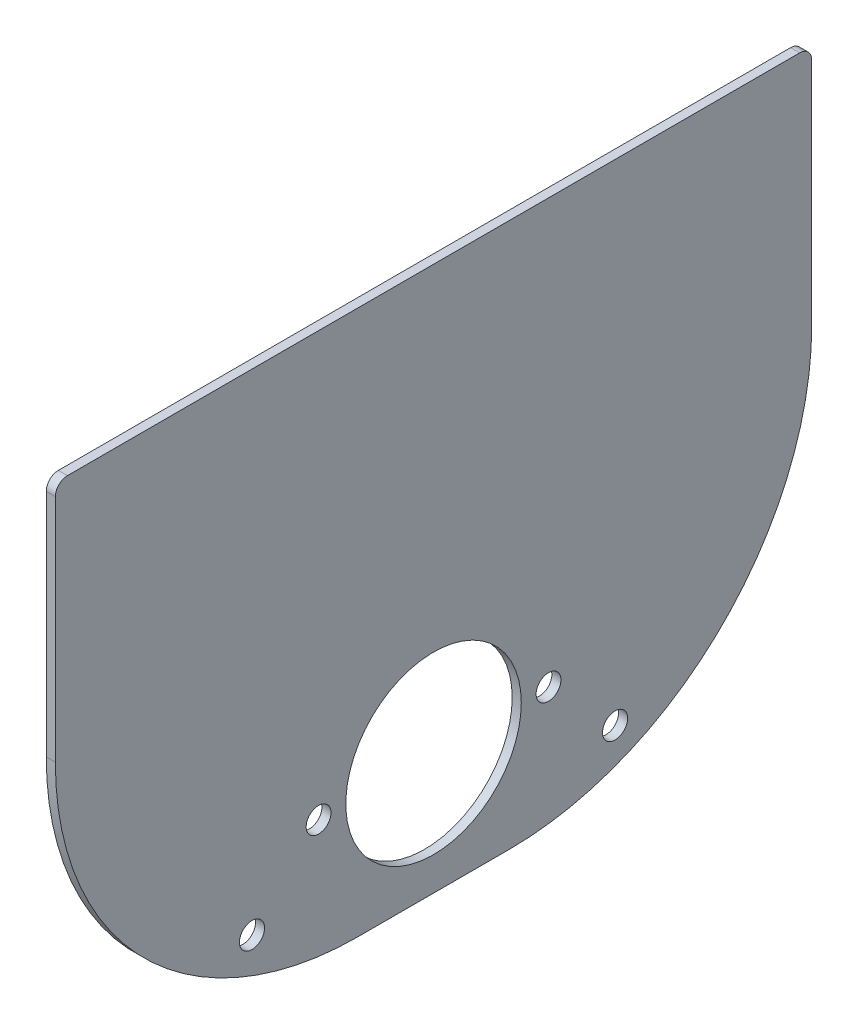
SolidWorks part; units mm, degrees
material "AISI 1020"
ref_plane "Спереди" through (0, 0, 0) normal (0, 0, 1) x (1, 0, 0)
ref_plane "Сверху" through (0, 0, 0) normal (0, 1, 0) x (1, 0, 0)
ref_plane "Справа" through (0, 0, 0) normal (1, 0, 0) x (0, 0, -1)
sketch "Эскиз1" plane through (0, 0, 0) normal (1, 0, 0) x (0, 0, -1)
  line L0 (0, 0) -> (0, -24.542) construction
  line L1 (-121, 140) -> (121, 140)
  line L2 (-125, 136) -> (-125, 60)
  line L3 (-25, -40) -> (25, -40)
  line L4 (125, 136) -> (125, 60)
  line L5 (-125, 140) -> (125, -40) construction
  line L6 (-125, -40) -> (125, 140) construction
  circle A0 centre (0, 0) radius 29
  circle A1 centre (38, 0) radius 4.1
  circle A2 centre (-38, 0) radius 4.1
  arc A3 (25, -40) -> (125, 60) centre (25, 60) ccw
  arc A4 (-125, 60) -> (-25, -40) centre (-25, 60) ccw
  arc A5 (121, 140) -> (125, 136) centre (121, 136) cw
  arc A6 (-121, 140) -> (-125, 136) centre (-121, 136) ccw
  circle A7 centre (-60, -22) radius 4.15
  circle A8 centre (60, -22) radius 4.15
  circle A13 centre (0, 0) radius 29 construction
  point P7 (0, 50)
  dimension "D2" = 8.2
  dimension "D7" = 100
  dimension "D8" = 4
  dimension "D11" = 8.3
  dimension "D3" = 76
  dimension "D4" = 140
  dimension "D5" = 250
  dimension "D6" = 40
  dimension "D9" = 60
  dimension "D10" = 22
extrude "Бобышка-Вытянуть1" add sketch "Эскиз1" along normal blind 3
